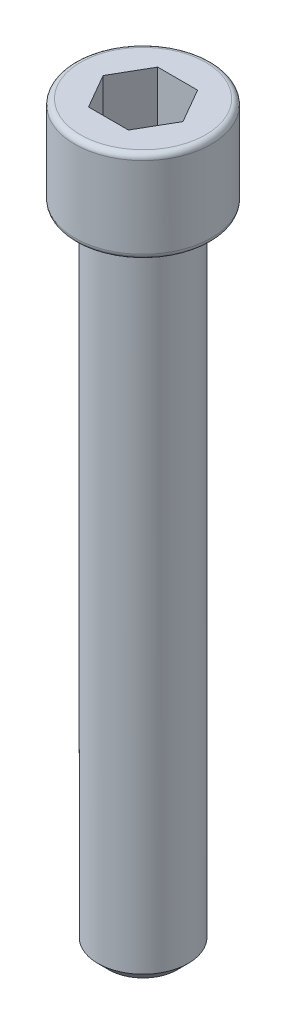
SolidWorks part; units mm, degrees
ref_plane "Front Plane" through (0, 0, 0) normal (0, 0, 1) x (1, 0, 0)
ref_plane "Top Plane" through (0, 0, 0) normal (0, 1, 0) x (1, 0, 0)
ref_plane "Right Plane" through (0, 0, 0) normal (1, 0, 0) x (0, 0, -1)
sketch "Sketch1" plane through (0, 0, 0) normal (0, 0, 1) x (1, 0, 0)
  line L0 (0, 0) -> (0, 57.6044) construction
  line L1 (0, 0) -> (0, 50.8)
  line L2 (0, 50.8) -> (-4.699, 50.8)
  line L3 (-4.699, 50.8) -> (-4.699, 44.45)
  line L4 (-4.699, 44.45) -> (-3.1115, 44.45)
  line L5 (-3.1115, 44.45) -> (-3.1115, 0)
  line L6 (-3.1115, 0) -> (0, 0)
  dimension "D1" = 6.35
  dimension "D2" = 6.223
  dimension "D3" = 50.8
  dimension "D4" = 9.398
revolve "Revolve1" add sketch "Sketch1" angle 360 about L0
sketch "Sketch2" plane through (0, 50.8, 0) normal (0, 1, 0) x (1, 0, 0)
  line L0 (0, 0) -> (2.3879, 0) construction
  line L1 (2.7496, 0) -> (1.3748, 2.3812)
  line L2 (1.3748, 2.3812) -> (-1.3748, 2.3812)
  line L3 (-1.3748, 2.3812) -> (-2.7496, 0)
  line L4 (-2.7496, 0) -> (-1.3748, -2.3812)
  line L5 (-1.3748, -2.3812) -> (1.3748, -2.3812)
  line L6 (1.3748, -2.3812) -> (2.7496, 0)
  circle A0 centre (0, 0) radius 2.3812 construction
  dimension "D1" = 4.7625
extrude "Extrude1" cut sketch "Sketch2" against normal blind 3.81
fillet "Fillet1" radius 0.381 2 edges at (0, 44.45, -4.699) (0, 50.8, -4.699)
chamfer "Chamfer1" distance 0.762 angle 45 1 edges at (0, 0, -3.1115)
